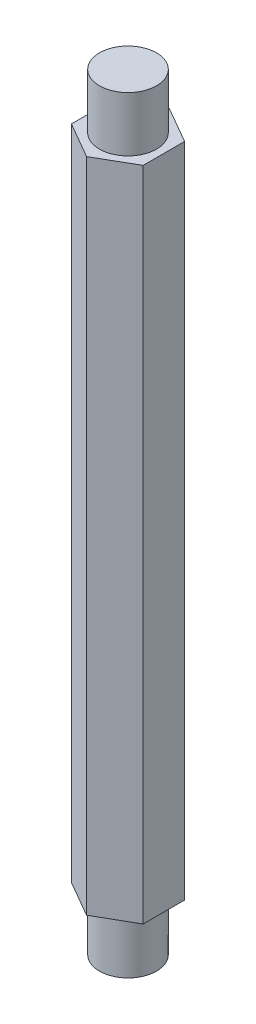
SolidWorks part; units mm, degrees
ref_plane "Front Plane" through (0, 0, 0) normal (0, 0, 1) x (1, 0, 0)
ref_plane "Top Plane" through (0, 0, 0) normal (0, 1, 0) x (1, 0, 0)
ref_plane "Right Plane" through (0, 0, 0) normal (1, 0, 0) x (0, 0, -1)
sketch "Sketch1" plane through (0, 0, 0) normal (0, 1, 0) x (1, 0, 0)
  line L1 (0, -2.396) -> (2.075, -1.198)
  line L2 (2.075, -1.198) -> (2.075, 1.198)
  line L3 (2.075, 1.198) -> (0, 2.396)
  line L4 (0, 2.396) -> (-2.075, 1.198)
  line L5 (-2.075, 1.198) -> (-2.075, -1.198)
  line L6 (-2.075, -1.198) -> (0, -2.396)
  circle A0 centre (0, 0) radius 1.65
  circle A1 centre (0, 0) radius 2.075 construction
  dimension "D1" = 3.3
  dimension "D2" = 4.15
extrude "Boss-Extrude1" add sketch "Sketch1" along normal blind 38
sketch "Sketch2" plane through (0, 0, 0) normal (0, -1, 0) x (1, 0, 0)
  circle A0 centre (0, 0) radius 1.65
extrude "Boss-Extrude2" add sketch "Sketch2" along normal blind 3.175 separate body
sketch "Sketch3" plane through (0, 38, 0) normal (0, 1, 0) x (1, 0, 0)
  circle A0 centre (0, 0) radius 1.65
extrude "Boss-Extrude3" add sketch "Sketch3" along normal blind 3.175 separate body
